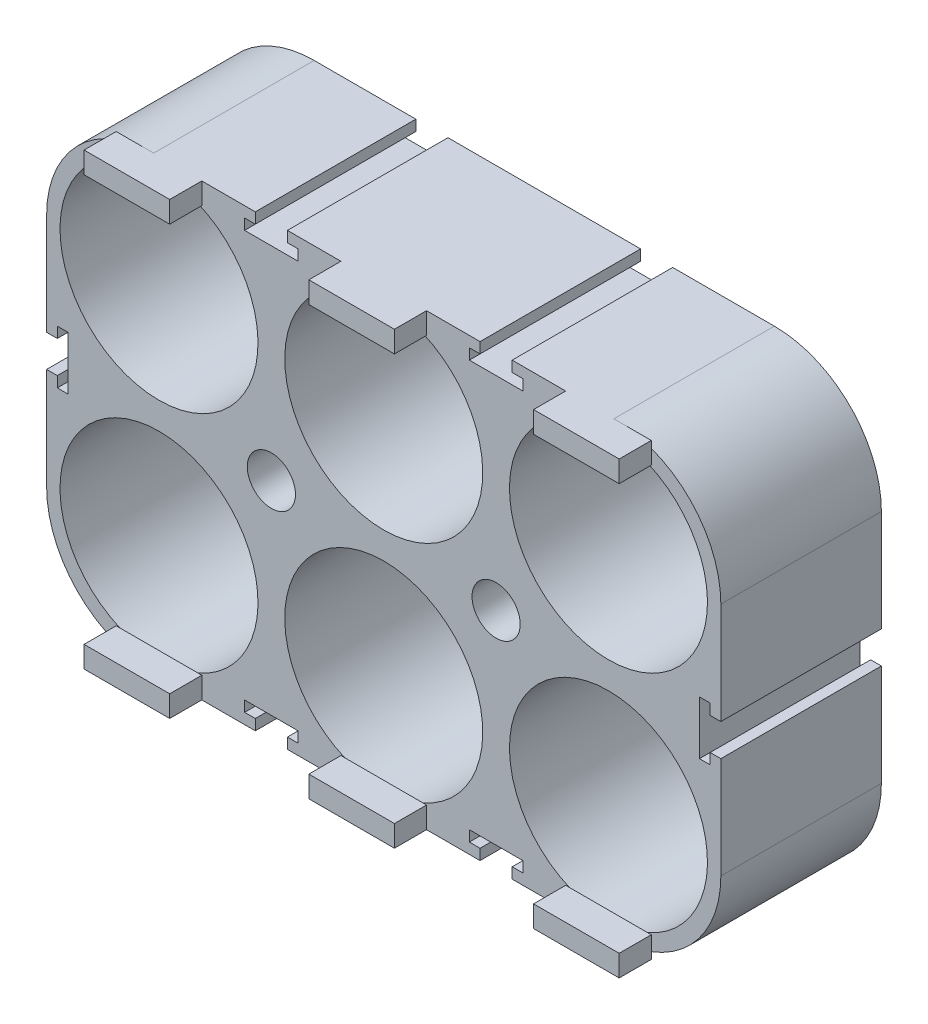
SolidWorks part; units mm, degrees
ref_plane "Front" through (0, 0, 0) normal (0, 0, 1) x (1, 0, 0)
ref_plane "Top" through (0, 0, 0) normal (0, 1, 0) x (1, 0, 0)
ref_plane "Right" through (0, 0, 0) normal (1, 0, 0) x (0, 0, -1)
sketch "Sketch1" plane through (0, 0, 0) normal (0, 0, 1) x (1, 0, 0)
  line L0 (31.5, 42) -> (31.5, 0) construction
  line L1 (0, 0) -> (63, 0)
  line L2 (0, 0) -> (0, 42)
  line L3 (0, 42) -> (63, 42)
  line L4 (63, 0) -> (63, 42)
  line L5 (10.5, 10.5) -> (10.5, 31.5) construction
  line L6 (52.5, 10.5) -> (52.5, 31.5) construction
  line L7 (31.5, 21) -> (10.5, 21) construction
  circle A0 centre (10.5, 31.5) radius 9.25
  circle A1 centre (10.5, 10.5) radius 9.25
  circle A2 centre (52.5, 31.5) radius 9.25
  circle A3 centre (52.5, 10.5) radius 9.25
  circle A4 centre (31.5, 31.5) radius 9.25
  circle A5 centre (31.5, 10.5) radius 9.25
  point P21 (10.5, 21)
  dimension "D4" = 18.5
  dimension "D1" = 63
  dimension "D2" = 42
  dimension "D3" = 21
  dimension "D5" = 21
  dimension "D6" = 21
extrude "Boss-Extrude1" add sketch "Sketch1" along normal blind 15
fillet "Fillet1" radius 10 4 edges at (0, 42, 7.5) (63, 42, 7.5) (63, 0, 7.5) (0, 0, 7.5)
sketch "Sketch3" plane through (0, 0, 15) normal (0, 0, 1) x (1, 0, 0)
  line L0 (31.5, 0) -> (31.5, 42) construction
  line L1 (10, 0) -> (53, 0) construction
  line L2 (53, 42) -> (10, 42) construction
  line L3 (0, 21) -> (63, 21) construction
  line L4 (27.5, 2) -> (35.5, 2)
  line L5 (27.5, 2) -> (27.5, 0)
  line L6 (27.5, 0) -> (35.5, 0)
  line L7 (35.5, 2) -> (35.5, 0)
  line L8 (27.5, 2) -> (35.5, 0) construction
  line L9 (27.5, 0) -> (35.5, 2) construction
  line L10 (56.5, 2) -> (48.5, 2)
  line L11 (56.5, 2) -> (56.5, 0)
  line L12 (56.5, 0) -> (48.5, 0)
  line L13 (48.5, 2) -> (48.5, 0)
  line L14 (56.5, 2) -> (48.5, 0) construction
  line L15 (56.5, 0) -> (48.5, 2) construction
  line L16 (14.5, 2) -> (6.5, 2)
  line L17 (14.5, 2) -> (14.5, 0)
  line L18 (14.5, 0) -> (6.5, 0)
  line L19 (6.5, 2) -> (6.5, 0)
  line L20 (14.5, 2) -> (6.5, 0) construction
  line L21 (14.5, 0) -> (6.5, 2) construction
  line L22 (0, 32) -> (0, 10) construction
  line L23 (63, 10) -> (63, 32) construction
  line L24 (6.5, 40) -> (6.5, 42)
  line L25 (14.5, 42) -> (6.5, 42)
  line L26 (14.5, 40) -> (6.5, 40)
  line L27 (14.5, 40) -> (14.5, 42)
  line L28 (27.5, 40) -> (27.5, 42)
  line L29 (27.5, 42) -> (35.5, 42)
  line L30 (27.5, 40) -> (35.5, 40)
  line L31 (35.5, 40) -> (35.5, 42)
  line L32 (48.5, 40) -> (48.5, 42)
  line L33 (56.5, 40) -> (56.5, 42)
  line L34 (56.5, 42) -> (48.5, 42)
  line L35 (56.5, 40) -> (48.5, 40)
  point P6 (31.5, 1)
  point P11 (52.5, 1)
  point P16 (10.5, 1)
  dimension "D1" = 21
  dimension "D2" = 21
  dimension "D3" = 8
  dimension "D4" = 2
extrude "Boss-Extrude2" add sketch "Sketch3" along normal blind 7
hole_wizard "M4 Clearance Hole1" positions "Sketch4" profile "Sketch5" hole size "M4" standard "ANSI Metric" end condition through all
sketch "Sketch4" plane through (0, 0, 15) normal (0, 0, 1) x (1, 0, 0)
  line L0 (0, 32) -> (0, 10) construction
  point P0 (21, 21)
  point P2 (42, 21)
  point P9 (0, 21)
  dimension "D1" = 21
  dimension "D2" = 21
sketch "Sketch5" plane through (21, 21, 15) normal (1, 0, 0) x (0, -1, 0)
  line L0 (0, 0) -> (0, 15)
  line L1 (0, 15) -> (2.25, 15)
  line L2 (2.25, 15) -> (2.25, 0)
  line L5 (2.25, 0) -> (0, 0)
  line L11 (0, -6.35) -> (0, 107.95) construction
  dimension "Thru Hole Dia." = 4.5
  dimension "Thru Hole Depth" = 15
sketch "Sketch6" plane through (0, 0, 0) normal (0, 0, -1) x (-1, 0, 0)
  line L0 (-63, 21) -> (0, 21) construction
  line L1 (-63, 10) -> (-63, 32) construction
  line L2 (0, 32) -> (0, 10) construction
  line L3 (0, 21) -> (-42, 21) construction
  line L4 (-42, 21) -> (-42, 42) construction
  line L5 (-53, 42) -> (-10, 42) construction
  line L6 (-21, 21) -> (-21, 42) construction
  line L7 (-40.5, 41) -> (-39.5, 41)
  line L9 (-43.5, 41) -> (-43.5, 42)
  line L10 (-43.5, 42) -> (-40.5, 42)
  line L11 (-40.5, 41) -> (-40.5, 42)
  line L12 (-43.5, 41) -> (-40.5, 42) construction
  line L13 (-43.5, 42) -> (-40.5, 41) construction
  line L14 (-44.5, 40) -> (-39.5, 40)
  line L15 (-44.5, 40) -> (-44.5, 41)
  line L16 (-44.5, 41) -> (-43.5, 41)
  line L17 (-39.5, 40) -> (-39.5, 41)
  line L18 (-44.5, 40) -> (-39.5, 41) construction
  line L19 (-44.5, 41) -> (-39.5, 40) construction
  line L20 (-19.5, 41) -> (-18.5, 41)
  line L21 (-22.5, 41) -> (-22.5, 42)
  line L22 (-22.5, 42) -> (-19.5, 42)
  line L23 (-19.5, 41) -> (-19.5, 42)
  line L24 (-22.5, 41) -> (-19.5, 42) construction
  line L25 (-22.5, 42) -> (-19.5, 41) construction
  line L26 (-23.5, 40) -> (-18.5, 40)
  line L27 (-23.5, 40) -> (-23.5, 41)
  line L28 (-23.5, 41) -> (-22.5, 41)
  line L29 (-18.5, 40) -> (-18.5, 41)
  line L30 (-23.5, 40) -> (-18.5, 41) construction
  line L31 (-23.5, 41) -> (-18.5, 40) construction
  line L32 (-44.5, 1) -> (-43.5, 1)
  line L33 (-44.5, 2) -> (-44.5, 1)
  line L34 (-43.5, 1) -> (-43.5, 0)
  line L35 (-44.5, 1) -> (-39.5, 2) construction
  line L36 (-44.5, 2) -> (-39.5, 1) construction
  line L37 (-43.5, 0) -> (-40.5, 1) construction
  line L38 (-43.5, 1) -> (-40.5, 0) construction
  line L39 (-39.5, 2) -> (-39.5, 1)
  line L40 (-44.5, 2) -> (-39.5, 2)
  line L41 (-40.5, 1) -> (-40.5, 0)
  line L42 (-43.5, 0) -> (-40.5, 0)
  line L43 (-40.5, 1) -> (-39.5, 1)
  line L44 (-18.5, 2) -> (-18.5, 1)
  line L45 (-19.5, 1) -> (-19.5, 0)
  line L46 (-19.5, 1) -> (-18.5, 1)
  line L47 (-23.5, 1) -> (-18.5, 2) construction
  line L48 (-23.5, 2) -> (-18.5, 1) construction
  line L49 (-22.5, 0) -> (-19.5, 1) construction
  line L50 (-22.5, 1) -> (-19.5, 0) construction
  line L51 (-23.5, 1) -> (-22.5, 1)
  line L52 (-23.5, 2) -> (-23.5, 1)
  line L53 (-23.5, 2) -> (-18.5, 2)
  line L54 (-22.5, 0) -> (-19.5, 0)
  line L55 (-22.5, 1) -> (-22.5, 0)
  line L56 (-31.5, 0) -> (-31.5, 42) construction
  line L57 (-62, 19.5) -> (-63, 19.5)
  line L59 (-62, 22.5) -> (-63, 22.5)
  line L60 (-63, 19.5) -> (-63, 22.5)
  line L61 (-62, 19.5) -> (-63, 22.5) construction
  line L62 (-62, 22.5) -> (-63, 19.5) construction
  line L63 (-61, 18.5) -> (-62, 18.5)
  line L64 (-61, 18.5) -> (-61, 23.5)
  line L65 (-61, 23.5) -> (-62, 23.5)
  line L66 (-62, 18.5) -> (-62, 19.5)
  line L67 (-61, 18.5) -> (-62, 23.5) construction
  line L68 (-61, 23.5) -> (-62, 18.5) construction
  line L69 (-10, 0) -> (-53, 0) construction
  line L70 (-62, 22.5) -> (-62, 23.5)
  line L71 (-1, 22.5) -> (-1, 23.5)
  line L72 (-2, 23.5) -> (-1, 23.5)
  line L73 (-1, 22.5) -> (0, 22.5)
  line L74 (-2, 23.5) -> (-1, 18.5) construction
  line L75 (-2, 18.5) -> (-1, 23.5) construction
  line L76 (-1, 22.5) -> (0, 19.5) construction
  line L77 (-1, 19.5) -> (0, 22.5) construction
  line L78 (-1, 18.5) -> (-1, 19.5)
  line L79 (-2, 18.5) -> (-2, 23.5)
  line L80 (-2, 18.5) -> (-1, 18.5)
  line L81 (0, 19.5) -> (0, 22.5)
  line L82 (-1, 19.5) -> (0, 19.5)
  point P14 (-42, 41.5)
  point P19 (-42, 40.5)
  point P24 (-21, 41.5)
  point P29 (-21, 40.5)
  point P34 (-61.5, 21)
  point P53 (-62.5, 21)
  dimension "D1" = 3
  dimension "D2" = 5
  dimension "D3" = 1
  dimension "D4" = 1
extrude "Cut-Extrude1" cut sketch "Sketch6" against normal through all
sketch "Sketch7" plane through (0, 0, 22) normal (0, 0, 1) x (1, 0, 0)
  line L1 (-26.5416, 54.1311) -> (89.5416, 54.1311)
  line L2 (-26.5416, 54.1311) -> (-26.5416, -33.1311)
  line L3 (-26.5416, -33.1311) -> (89.5416, -33.1311)
  line L4 (89.5416, 54.1311) -> (89.5416, -33.1311)
  line L5 (-26.5416, 54.1311) -> (89.5416, -33.1311) construction
  line L6 (-26.5416, -33.1311) -> (89.5416, 54.1311) construction
  point P0 (31.5, 10.5)
extrude "Cut-Extrude2" cut sketch "Sketch7" against normal offset from surface (4 mm away) 3 up to face at (31.5, 21, 15)
